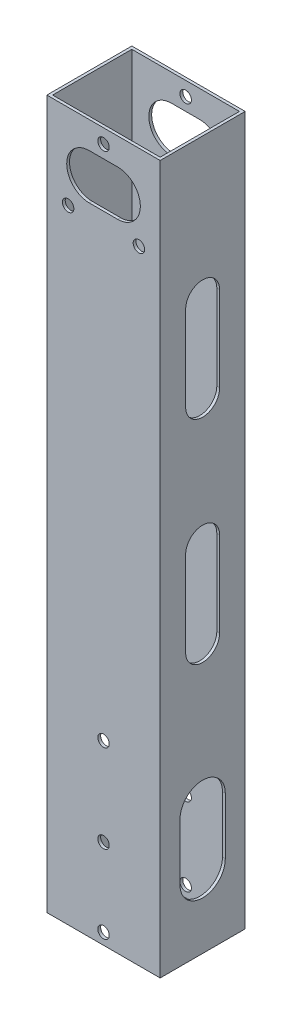
SolidWorks part; units mm, degrees
material "6063-T5"
ref_plane "前视基准面" through (0, 0, 0) normal (0, 0, 1) x (1, 0, 0)
ref_plane "上视基准面" through (0, 0, 0) normal (0, 1, 0) x (1, 0, 0)
ref_plane "右视基准面" through (0, 0, 0) normal (1, 0, 0) x (0, 0, -1)
other "Configuration Table"
sketch "草图1" plane through (0, 0, 0) normal (0, 1, 0) x (1, 0, 0)
  line L1 (-20, -15) -> (20, -15)
  line L2 (-20, -15) -> (-20, 15)
  line L3 (-20, 15) -> (20, 15)
  line L4 (20, -15) -> (20, 15)
  line L5 (-20, -15) -> (20, 15) construction
  line L6 (-20, 15) -> (20, -15) construction
  point P0 (0, 0)
  dimension "D1" = 40
  dimension "D2" = 30
extrude "凸台-拉伸1" add sketch "草图1" along normal mid plane 250
sketch "草图2" plane through (0, 0, 0) normal (0, 1, 0) x (1, 0, 0)
  line L8 (19, -14) -> (19, 14)
  line L9 (19, 14) -> (-19, 14)
  line L10 (-19, 14) -> (-19, -14)
  line L11 (-19, -14) -> (19, -14)
  line L12 (19, -14) -> (19, 14)
  line L13 (19, 14) -> (-19, 14)
  line L14 (-19, 14) -> (-19, -14)
  line L15 (-19, -14) -> (19, -14)
  dimension "D1" = 1
extrude "切除-拉伸1" cut sketch "草图2" against normal through all both and the other way through all
sketch "草图3" plane through (0, 0, 15) normal (0, 0, 1) x (1, 0, 0)
  line L0 (0, -62.433) -> (0, -121) construction
  line L1 (-20, -125) -> (20, -125) construction
  circle A0 centre (0, -62.433) radius 2.025
  circle A1 centre (0, -93.433) radius 2.025
  circle A2 centre (0, -121) radius 2.025
  dimension "D1" = 4.05
  dimension "D2" = 4
  dimension "D3" = 27.567
  dimension "D4" = 31
extrude "切除-拉伸2" cut sketch "草图3" against normal through all both
sketch "草图4" plane through (0, 0, -15) normal (0, 0, -1) x (-1, 0, 0)
  circle A0 centre (0, 120) radius 2.025
  circle A1 centre (12.5, 95) radius 2.025
  circle A2 centre (-12.5, 95) radius 2.025
  dimension "D1" = 4.05
extrude "切除-拉伸3" cut sketch "草图4" against normal through all both
sketch "草图5" plane through (20, 0, 0) normal (1, 0, 0) x (0, 0, -1)
  line L0 (0, -100) -> (0, -80) construction
  line L1 (-8, -100) -> (-8, -80)
  line L2 (8, -100) -> (8, -80)
  line L3 (-15, -125) -> (15, -125) construction
  arc A0 (-8, -100) -> (8, -100) centre (0, -100) ccw
  arc A1 (8, -80) -> (-8, -80) centre (0, -80) ccw
  point P3 (0, -90)
  dimension "D1" = 8
  dimension "D2" = 20
  dimension "D3" = 35
extrude "切除-拉伸4" cut sketch "草图5" against normal through all both and the other way through all
sketch "草图6" plane through (0, 0, -15) normal (0, 0, -1) x (-1, 0, 0)
  line L0 (-5, 107.5) -> (5, 107.5) construction
  line L1 (-5, 115.5) -> (5, 115.5)
  line L2 (-5, 99.5) -> (5, 99.5)
  line L3 (-20, 125) -> (-20, -125) construction
  arc A0 (-5, 115.5) -> (-5, 99.5) centre (-5, 107.5) ccw
  arc A1 (5, 99.5) -> (5, 115.5) centre (5, 107.5) ccw
  circle A3 centre (12.5, 95) radius 2.025 construction
  point P2 (0, 107.5)
  dimension "D1" = 8
  dimension "D2" = 10
  dimension "D3" = 20
  dimension "D4" = 12.5
extrude "切除-拉伸5" cut sketch "草图6" against normal through all both
sketch "草图7" plane through (20, 0, 0) normal (1, 0, 0) x (0, 0, -1)
  line L0 (0, 45) -> (0, 75) construction
  line L1 (-6, 45) -> (-6, 75)
  line L2 (6, 45) -> (6, 75)
  line L3 (0, -30) -> (0, 0) construction
  line L4 (-6, -30) -> (-6, 0)
  line L5 (6, -30) -> (6, 0)
  arc A0 (-6, 45) -> (6, 45) centre (0, 45) ccw
  arc A1 (6, 75) -> (-6, 75) centre (0, 75) ccw
  arc A2 (-6, -30) -> (6, -30) centre (0, -30) ccw
  arc A3 (6, 0) -> (-6, 0) centre (0, 0) ccw
  point P3 (0, 60)
  point P8 (0, -15)
  point P15 (0, -51.7323)
  point P16 (0, 87.5799)
  point P17 (0, 13.2253)
  point P18 (0, 0)
  dimension "D2" = 6
  dimension "D1" = 30
  dimension "D3" = 45
extrude "切除-拉伸6" cut sketch "草图7" against normal through all both and the other way through all
